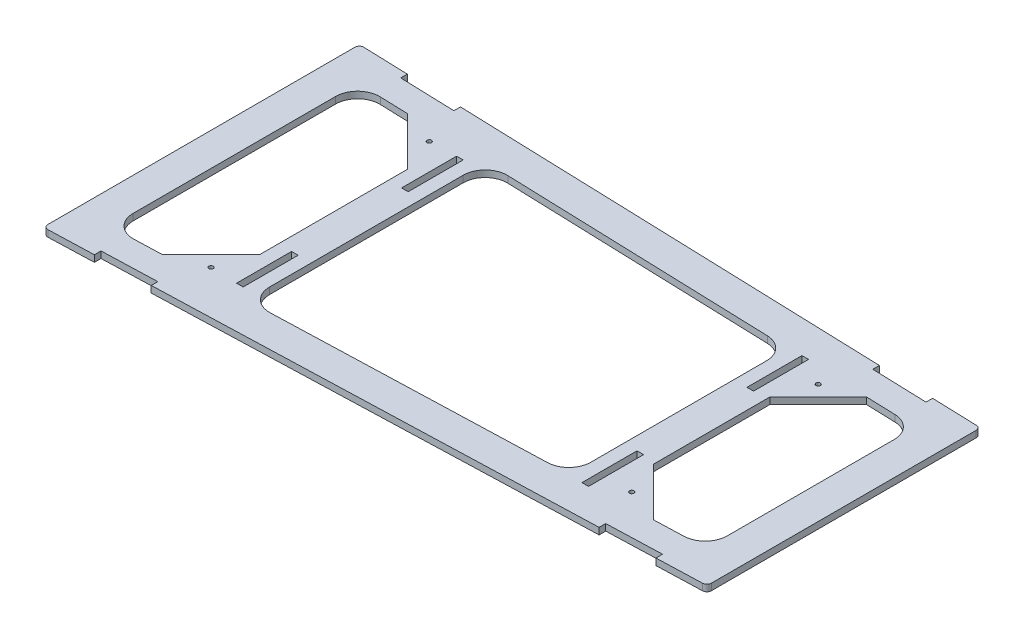
SolidWorks part; units mm, degrees
ref_plane "Front Plane" through (0, 0, 0) normal (0, 0, 1) x (1, 0, 0)
ref_plane "Top Plane" through (0, 0, 0) normal (0, 1, 0) x (1, 0, 0)
ref_plane "Right Plane" through (0, 0, 0) normal (1, 0, 0) x (0, 0, -1)
sketch "Sketch1" plane through (0, 0, 0) normal (0, 1, 0) x (1, 0, 0)
  line L0 (0, 71.865) -> (0, -71.865)
  line L1 (0, 71.865) -> (292, 62.13)
  line L2 (292, 62.13) -> (292, -62.13)
  line L3 (292, -62.13) -> (0, -71.865)
  line L4 (15, 56.3566) -> (60, 54.8563)
  line L5 (277, 47.6218) -> (277, -47.6218)
  line L6 (277, -47.6218) -> (232, -49.122)
  line L7 (15, 56.3566) -> (15, -56.3566)
  line L8 (60, 54.8563) -> (60, -54.8563)
  line L9 (75, 54.3562) -> (75, -54.3562)
  line L10 (217, 49.6221) -> (217, -49.6221)
  line L11 (232, 49.122) -> (232, -49.122)
  line L12 (60, 54.8563) -> (75, 54.3562) construction
  line L13 (75, 54.3562) -> (217, 49.6221)
  line L14 (15, 56.3566) -> (277, 47.6218) construction
  line L15 (75, -54.3562) -> (60, -54.8563) construction
  line L16 (60, -54.8563) -> (15, -56.3566)
  line L17 (277, -47.6218) -> (15, -56.3566) construction
  line L18 (232, -49.122) -> (217, -49.6221) construction
  line L19 (217, -49.6221) -> (75, -54.3562)
  line L20 (217, 49.6221) -> (232, 49.122) construction
  line L21 (232, 49.122) -> (277, 47.6218)
  line L22 (67.5, 54.6063) -> (67.5, -54.6063) construction
  line L23 (224.5, 49.3721) -> (224.5, -49.3721) construction
  line L24 (0, 71.865) -> (67.4455, 69.6164) construction
  point P0 (292, 0)
  point P3 (0, 0)
  dimension "D1" = 143.73
  dimension "D2" = 292
  dimension "D3" = 124.26
  dimension "D5" = 15
  dimension "D6" = 15
  dimension "D7" = 60
  dimension "D8" = 60
  dimension "D4" = 15
extrude "Boss-Extrude1" add sketch "Sketch1" along normal blind 3
fillet "Fillet1" radius 2 4 edges at (292, 1.5, -62.13) (292, 1.5, 62.13) (0, 1.5, 71.865) (0, 1.5, -71.865)
fillet "Fillet2" radius 10 12 edges at (277, 1.5, 47.6218) (277, 1.5, -47.6218) (232, 1.5, -49.122) (232, 1.5, 49.122) (217, 1.5, 49.6221) (217, 1.5, -49.6221) (75, 1.5, 54.3562) (15, 1.5, 56.3566) (60, 1.5, 54.8563) (60, 1.5, -54.8563) (75, 1.5, -54.3562) (15, 1.5, -56.3566)
sketch "Sketch2" plane through (0, 3, 0) normal (0, 1, 0) x (1, 0, 0)
  line L0 (22.5, 71.1149) -> (22.5, 68.1149)
  line L1 (290.0666, 62.1945) -> (2.0666, 71.7961) construction
  line L2 (22.5, 68.1149) -> (47.5, 67.2814)
  line L3 (47.5, 67.2814) -> (47.5, 70.2814)
  line L4 (0, 69.7972) -> (0, -69.7972) construction
  line L5 (244.5, 63.7136) -> (244.5, 60.7136)
  line L6 (244.5, 60.7136) -> (269.5, 59.8801)
  line L7 (269.5, 59.8801) -> (269.5, 62.8801)
  line L8 (292, -60.1956) -> (292, 60.1956) construction
  line L9 (60, 0) -> (75, 0) construction
  line L10 (66, 50) -> (69, 50)
  line L11 (66, 50) -> (66, 25)
  line L12 (66, 25) -> (69, 25)
  line L13 (69, 50) -> (69, 25)
  line L14 (223, 50) -> (226, 50)
  line L15 (223, 50) -> (223, 25)
  line L16 (223, 25) -> (226, 25)
  line L17 (226, 50) -> (226, 25)
  line L18 (60, -45.1842) -> (60, 45.1842) construction
  line L19 (75, 44.0173) -> (75, -44.0173) construction
  line L20 (217, 0) -> (232, 0) construction
  line L21 (217, -39.9499) -> (217, 39.9499) construction
  line L22 (232, 38.7831) -> (232, -38.7831) construction
  line L24 (0, 50) -> (3, 50) construction
  line L25 (0, 50) -> (0, 25) construction
  line L26 (0, 25) -> (3, 25) construction
  line L27 (3, 50) -> (3, 25) construction
  line L28 (292, 50) -> (289, 50) construction
  line L29 (292, 50) -> (292, 25) construction
  line L30 (292, 25) -> (289, 25) construction
  line L31 (289, 50) -> (289, 25) construction
  point P4 (35, 67.6981)
  point P9 (257, 60.2969)
  point P36 (67.5, 25)
  point P37 (67.5, 0)
  point P38 (224.5, 0)
  point P39 (224.5, 25)
  line M18 (290.0666, 62.1945) -> (2.0666, 71.7961)
  dimension "D1" = 25
  dimension "D2" = 35
  dimension "D3" = 3
  dimension "D4" = 3
  dimension "D5" = 35
  dimension "D6" = 25
  dimension "D7" = 3
  dimension "D8" = 3
  dimension "D9" = 25
  dimension "D10" = 25
  dimension "D11" = 25
  dimension "D12" = 25
  dimension "D13" = 3
  dimension "D14" = 25
  dimension "D15" = 25
  dimension "D16" = 3
  dimension "D17" = 25
  dimension "D18" = 25
extrude "Cut-Extrude1" cut sketch "Sketch2" against normal blind 10 contours L2 L3 L0 M18 | L13 L10 L11 L12 | L6 L7 L5 M18 | L15 L16 L17 L14 | L25 L24 L27 L26 | L29 L28 L31 L30
mirror "Mirror1" about plane through (0, 0, 0) normal (0, 0, 1) of "Cut-Extrude1"
sketch "Sketch3" plane through (0, 3, 0) normal (0, 1, 0) x (1, 0, 0)
  line L0 (38, 55.5898) -> (60, 33.5898)
  line L1 (50.3332, 55.1786) -> (25.3332, 56.0121) construction
  line L2 (60, -45.1842) -> (60, 45.1842) construction
  line L3 (60, 33.5898) -> (61.5098, 56.6918)
  line L4 (61.5098, 56.6918) -> (38, 55.5898)
  line L5 (232, 26.3885) -> (254, 48.3885)
  line L6 (232, 38.7831) -> (232, -38.7831) construction
  line L7 (267.3332, 47.944) -> (242.3332, 48.7775) construction
  line L8 (254, 48.3885) -> (229.7017, 51.0442)
  line L9 (229.7017, 51.0442) -> (232, 26.3885)
  line L10 (38, 55.5898) -> (60, 55.5898) construction
  line L11 (60, 55.5898) -> (60, 33.5898) construction
  line L12 (232, 26.3885) -> (232, 48.3885) construction
  line L13 (232, 48.3885) -> (254, 48.3885) construction
  line L14 (-1.65, 0) -> (1.65, 0) construction
  line L15 (254, -48.3885) -> (229.7017, -51.0442)
  line L16 (232, -26.3885) -> (254, -48.3885)
  line L17 (229.7017, -51.0442) -> (232, -26.3885)
  line L18 (60, -33.5898) -> (61.5098, -56.6918)
  line L19 (38, -55.5898) -> (60, -33.5898)
  line L20 (61.5098, -56.6918) -> (38, -55.5898)
  circle A0 centre (54, 49.5898) radius 1
  circle A1 centre (238, 42.3885) radius 1
  circle A2 centre (238, -42.3885) radius 1
  circle A3 centre (54, -49.5898) radius 1
  dimension "D5" = 2
  dimension "D8" = 2
  dimension "D1" = 22
  dimension "D2" = 22
  dimension "D3" = 22
  dimension "D4" = 22
  dimension "D6" = 6
  dimension "D7" = 6
  dimension "D9" = 6
  dimension "D10" = 6
extrude "Boss-Extrude2" add sketch "Sketch3" against normal blind 3
equation "\"D6@Sketch1\"=\"D5@Sketch1\""
